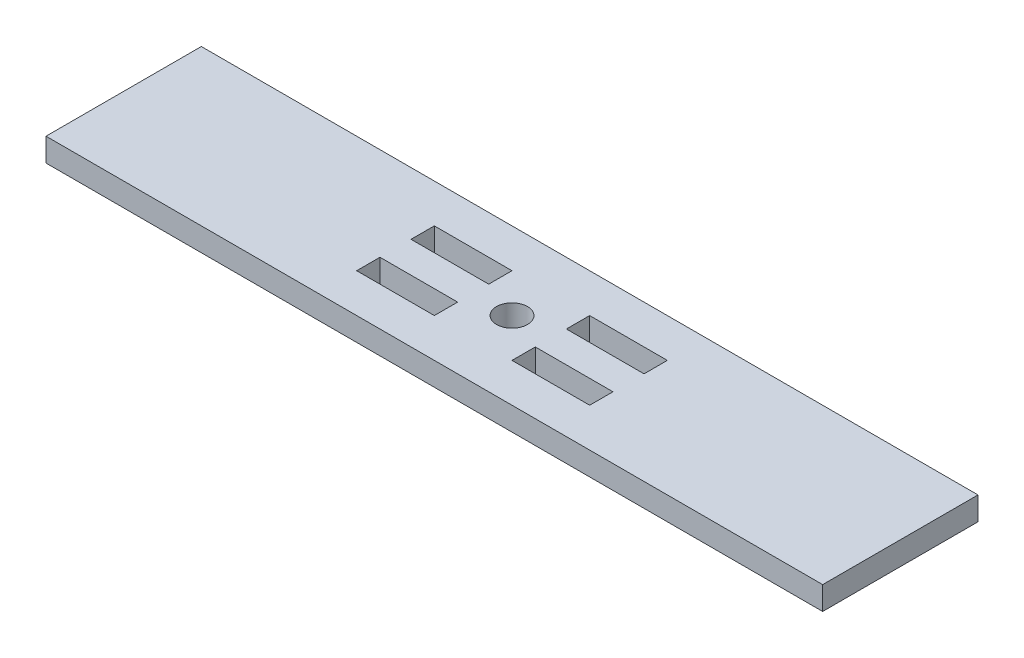
SolidWorks part; units mm, degrees
ref_plane "Front Plane" through (0, 0, 0) normal (0, 0, 1) x (1, 0, 0)
ref_plane "Top Plane" through (0, 0, 0) normal (0, 1, 0) x (1, 0, 0)
ref_plane "Right Plane" through (0, 0, 0) normal (1, 0, 0) x (0, 0, -1)
sketch "Sketch1" plane through (0, 0, 0) normal (0, 1, 0) x (1, 0, 0)
  line L1 (-9.8298, 5.8807) -> (40.1702, 5.8807)
  line L2 (-9.8298, 5.8807) -> (-9.8298, -4.1193)
  line L3 (-9.8298, -4.1193) -> (40.1702, -4.1193)
  line L4 (40.1702, 5.8807) -> (40.1702, -4.1193)
  point P4 (-9.8298, 5.8807)
  dimension "D1" = 10
  dimension "D2" = 50
extrude "Boss-Extrude1" add sketch "Sketch1" along normal blind 1.5
sketch "Sketch2" plane through (0, 1.5, 0) normal (0, 1, 0) x (1, 0, 0)
  line L4 (40.1702, 5.8807) -> (-9.8298, 5.8807) construction
  line L5 (15.1702, 5.8807) -> (15.1702, -4.1193) construction
  line L6 (-9.8298, 0.8807) -> (40.1702, 0.8807) construction
  line L7 (-9.8298, 5.8807) -> (-9.8298, -4.1193) construction
  line L8 (40.1702, -4.1193) -> (40.1702, 5.8807) construction
  circle A0 centre (15.1702, 0.8807) radius 1
  point P8 (2.2751, -0.4216)
  point P9 (2.2751, -0.3704)
  point P14 (0, 0)
  dimension "D1" = 2
sketch "Sketch3" plane through (0, 1.5, 0) normal (0, 1, 0) x (1, 0, 0)
  line L0 (15.1702, 5.8807) -> (15.1702, -4.1193) construction
  line L1 (7.6702, 3.3807) -> (12.6702, 3.3807)
  line L2 (7.6702, 3.3807) -> (7.6702, 1.8807)
  line L3 (7.6702, 1.8807) -> (12.6702, 1.8807)
  line L4 (12.6702, 3.3807) -> (12.6702, 1.8807)
  line L5 (17.6702, 1.8807) -> (22.6702, 1.8807)
  line L6 (17.6702, 1.8807) -> (17.6702, 3.3807)
  line L7 (17.6702, 3.3807) -> (22.6702, 3.3807)
  line L8 (22.6702, 1.8807) -> (22.6702, 3.3807)
  line L9 (22.6702, -1.6193) -> (17.6702, -1.6193)
  line L10 (22.6702, -1.6193) -> (22.6702, -0.1193)
  line L11 (22.6702, -0.1193) -> (17.6702, -0.1193)
  line L12 (17.6702, -1.6193) -> (17.6702, -0.1193)
  line L13 (12.6702, -1.6193) -> (7.6702, -1.6193)
  line L14 (12.6702, -1.6193) -> (12.6702, -0.1193)
  line L15 (12.6702, -0.1193) -> (7.6702, -0.1193)
  line L16 (7.6702, -1.6193) -> (7.6702, -0.1193)
  line L17 (-9.8298, 0.8807) -> (40.1702, 0.8807) construction
  point P16 (12.6702, 2.6307)
  dimension "D1" = 5
  dimension "D2" = 2.5
  dimension "D3" = 2
  dimension "D4" = 1
  dimension "D5" = 1.5
  dimension "D6" = 5
extrude "Cut-Extrude1" cut sketch "Sketch3" against normal blind 2
extrude "Cut-Extrude2" cut sketch "Sketch2" against normal blind 2 contours A0
equation "\"board_thickness\"=0.15"
equation "\"D5@Sketch3\"=\"board_thickness\""
